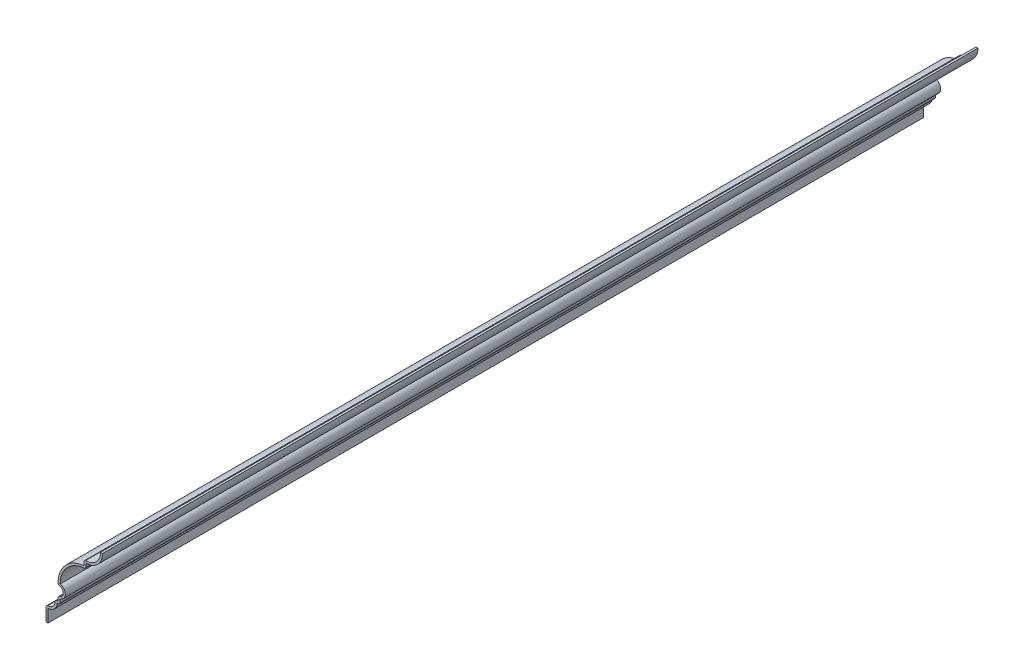
SolidWorks part; units mm, degrees
ref_plane "Front Plane" through (0, 0, 0) normal (0, 0, 1) x (1, 0, 0)
ref_plane "Top Plane" through (0, 0, 0) normal (0, 1, 0) x (1, 0, 0)
ref_plane "Right Plane" through (0, 0, 0) normal (1, 0, 0) x (0, 0, -1)
sketch "Sketch1" plane through (0, 0, 0) normal (0, 0, 1) x (1, 0, 0)
  line L0 (0, 0) -> (0, 53.975) construction
  line L1 (0, 0) -> (-33.655, 0) construction
  line L2 (-33.655, 0) -> (-33.655, 7.9375)
  line L3 (-28.0987, 13.4937) -> (-26.1938, 13.4937)
  line L4 (-26.1938, 13.4937) -> (-26.1938, 16.6687)
  line L5 (-10.3188, 40.4812) -> (-10.3188, 43.6562)
  line L6 (-34.925, 0) -> (-34.925, 9.4) construction
  line L7 (-29.5612, 14.7637) -> (-27.4638, 14.7637) construction
  line L8 (-27.4638, 14.7637) -> (-27.4638, 17.8651) construction
  line L9 (-11.5887, 41.7041) -> (-11.5887, 45.0158) construction
  line L10 (-26.1938, 24.6062) -> (-10.3187, 24.6062) construction
  line L11 (-10.3187, 24.6062) -> (-10.3188, 40.4812) construction
  arc A0 (-33.655, 7.9375) -> (-28.0987, 13.4937) centre (-33.655, 13.4937) ccw
  arc A1 (-26.1938, 16.6687) -> (-26.1938, 24.6062) centre (-27.0867, 20.6375) ccw
  arc A2 (-26.1938, 24.6062) -> (-10.3188, 40.4812) centre (-10.3187, 24.6062) cw
  arc A3 (-10.3188, 43.6562) -> (0, 53.975) centre (-10.3188, 53.975) ccw
  arc A4 (-34.925, 9.4) -> (-29.5612, 14.7637) centre (-33.655, 13.4937) ccw construction
  arc A5 (-33.655, 7.9375) -> (-28.0987, 13.4937) centre (-33.655, 13.4937) ccw construction
  arc A6 (-27.4223, 23.4153) -> (-11.5887, 41.7041) centre (-10.3187, 24.6062) cw construction
  arc A7 (-11.5887, 45.0158) -> (-1.27, 53.975) centre (-10.3188, 53.975) ccw construction
  arc A8 (-26.1938, 16.6687) -> (-26.1938, 24.6062) centre (-27.0867, 20.6375) ccw construction
  arc A9 (-27.4638, 17.8651) -> (-27.4223, 23.4153) centre (-27.0867, 20.6375) ccw construction
  dimension "D8" = 15.875
  dimension "D10" = 10.3187
  dimension "D2" = 5.5562
  dimension "D3" = 7.9375
  dimension "D4" = 34.925
  dimension "D5" = 3.175
  dimension "D6" = 7.9375
  dimension "D7" = 3.175
  dimension "D9" = 3.175
  dimension "D1" = 1.27
extrude "Extrude-Thin1" add sketch "Sketch1" against normal blind 539.75 thin thin type one direction reverse wall 1.27
fillet "Fillet1" radius 1.27 7 edges at (-34.925, 9.4, -269.875) (-29.5612, 14.7637, -269.875) (-26.1938, 13.4937, -269.875) (-27.4638, 17.8651, -269.875) (-27.4223, 23.4153, -269.875) (-10.3188, 40.4812, -269.875) (-11.5888, 45.0158, -269.875)
